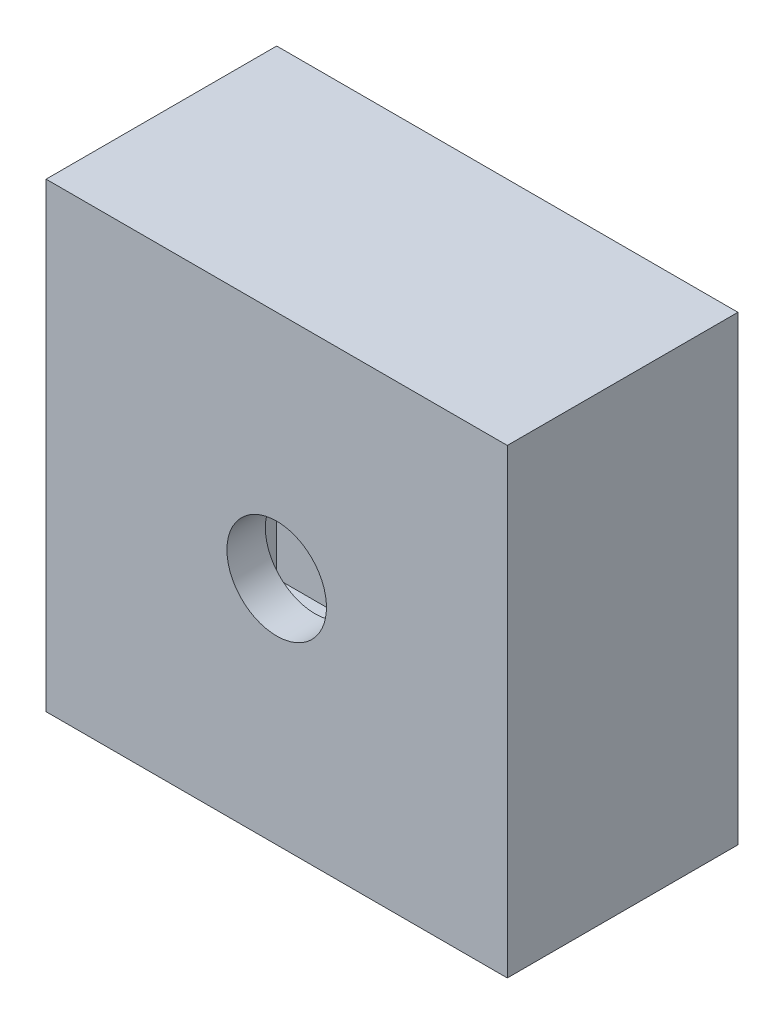
SolidWorks part; units mm, degrees
ref_plane "Front Plane" through (0, 0, 0) normal (0, 0, 1) x (1, 0, 0)
ref_plane "Top Plane" through (0, 0, 0) normal (0, 1, 0) x (1, 0, 0)
ref_plane "Right Plane" through (0, 0, 0) normal (1, 0, 0) x (0, 0, -1)
sketch "Sketch2" plane through (0, 0, 0) normal (0, 0, 1) x (1, 0, 0)
  line L1 (-600, 600) -> (600, 600)
  line L2 (-600, 600) -> (-600, -600)
  line L3 (-600, -600) -> (600, -600)
  line L4 (600, 600) -> (600, -600)
  line L5 (-600, 600) -> (600, -600) construction
  line L6 (-600, -600) -> (600, 600) construction
  point P0 (0, 0)
  dimension "D1" = 1200
extrude "Boss-Extrude1" add sketch "Sketch2" along normal blind 600
shell "Shell1" thickness 100
sketch "Sketch4" plane through (0, 0, 600) normal (0, 0, 1) x (1, 0, 0)
  line L4 (600, -600) -> (600, 600)
  line L5 (600, 600) -> (-600, 600)
  line L6 (-600, 600) -> (-600, -600)
  line L7 (-600, -600) -> (600, -600)
  line L8 (600, -600) -> (600, 600)
  line L9 (600, 600) -> (-600, 600)
  line L10 (-600, 600) -> (-600, -600)
  line L11 (-600, -600) -> (600, -600)
  dimension "D1" = 0
extrude "Boss-Extrude2" add sketch "Sketch4" against normal blind 100
sketch "Sketch5" plane through (0, 0, 0) normal (0, 0, -1) x (-1, 0, 0)
  circle A0 centre (0, 0) radius 129.5
  dimension "D1" = 259
extrude "Cut-Extrude2" cut sketch "Sketch5" against normal through all
sketch "Sketch7" plane through (0, 0, 0) normal (0, 0, -1) x (-1, 0, 0)
  line L0 (-600, 600) -> (600, 600) construction
  line L1 (65, 375) -> (-65, 375)
  line L2 (65, 375) -> (65, 245)
  line L3 (65, 245) -> (-65, 245)
  line L4 (-65, 375) -> (-65, 245)
  line L5 (65, 375) -> (-65, 245) construction
  line L6 (65, 245) -> (-65, 375) construction
  point P0 (0, 310)
  dimension "D1" = 290
  dimension "D2" = 600
  dimension "D3" = 130
extrude "Cut-Extrude3" cut sketch "Sketch7" against normal blind 146
pattern_circular "CirPattern1" count 4 over 360 about axis through (0, 0, 0) along (0, 0, 1) of "Cut-Extrude3"
sketch "Sketch8" plane through (0, -600, 0) normal (0, -1, 0) x (1, 0, 0)
  circle A0 centre (-344.3674, 324.291) radius 120
  dimension "D3" = 240
extrude "Cut-Extrude4" cut sketch "Sketch8" against normal up to surface (100 mm away) up to face at (0, -500, 300)
